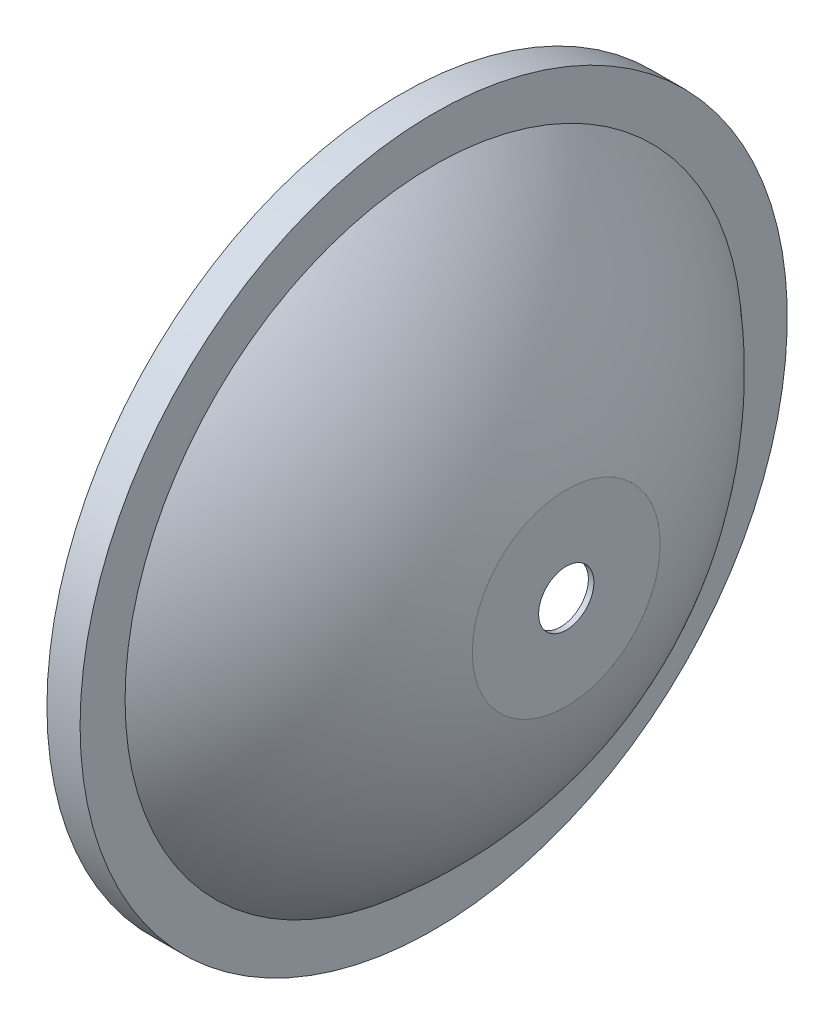
SolidWorks part; units mm, degrees
ref_plane "Front Plane" through (0, 0, 0) normal (0, 0, 1) x (1, 0, 0)
ref_plane "Top Plane" through (0, 0, 0) normal (0, 1, 0) x (1, 0, 0)
ref_plane "Right Plane" through (0, 0, 0) normal (1, 0, 0) x (0, 0, -1)
sketch "Sketch1" plane through (0, 0, 0) normal (0, 0, 1) x (1, 0, 0)
  line L1 (41, 64) -> (47, 64)
  line L2 (47, 64) -> (47, 55.857)
  line L3 (70.993, 17) -> (70.993, 5)
  line L5 (0, 0) -> (123.4294, 0) construction
  line L7 (41, 63) -> (46, 63)
  line L8 (46, 63) -> (46, 55.3895)
  line L9 (69.993, 16.8815) -> (69.993, 5)
  line L11 (69.993, 6) -> (42, 6) construction
  line L12 (70.993, 5) -> (41, 5) construction
  line L13 (42, 6) -> (42, 63) construction
  line L14 (41, 5) -> (41, 64) construction
  line L15 (41, 64) -> (41, 63)
  line L16 (70.993, 5) -> (69.993, 5)
  line L17 (69.993, 16.8815) -> (69.993, 6) construction
  line L18 (42, 63) -> (46, 63) construction
  arc A0 (47, 55.857) -> (70.993, 17) centre (0, 0) cw
  arc A1 (46, 55.3895) -> (69.993, 16.8815) centre (0, 0) cw
  point P14 (0, 0)
  dimension "D3" = 73
  dimension "D1" = 5
  dimension "D2" = 41
  dimension "D4" = 12
  dimension "D5" = 6
  dimension "D6" = 64
  dimension "D7" = 1
revolve "Revolve1" add sketch "Sketch1" angle 360 about L5
